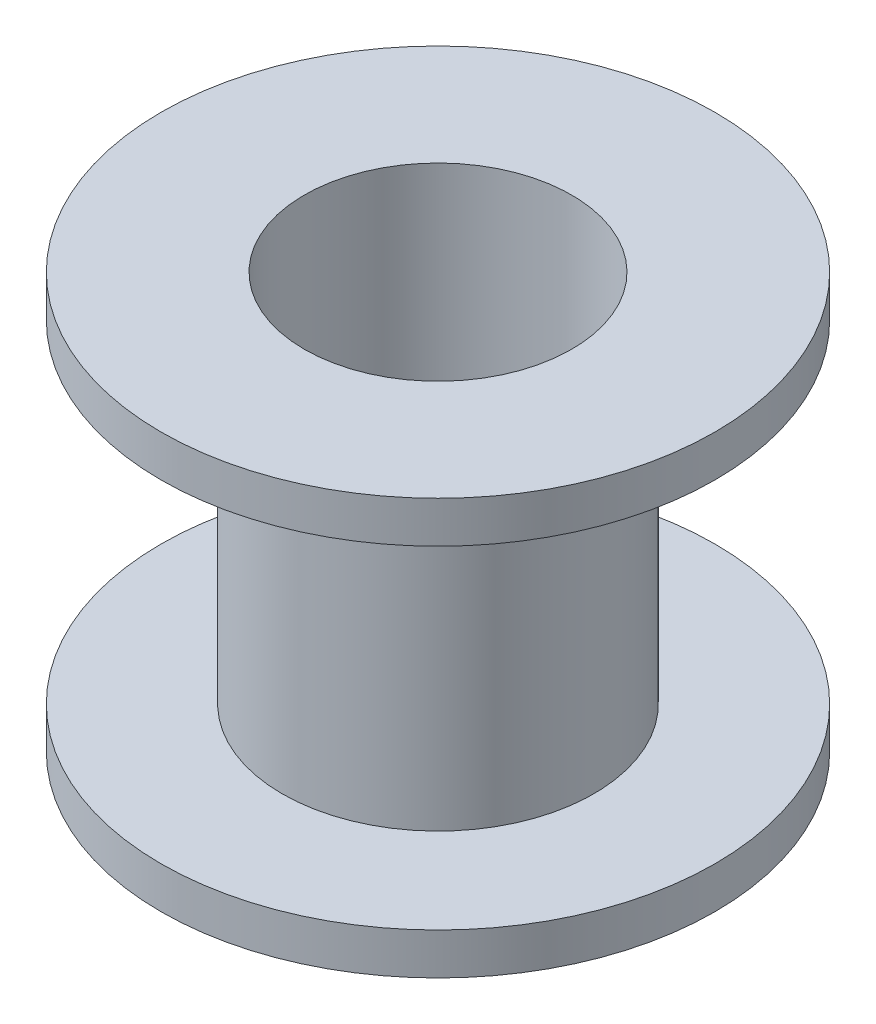
SolidWorks part; units mm, degrees
ref_plane "Front Plane" through (0, 0, 0) normal (0, 0, 1) x (1, 0, 0)
ref_plane "Top Plane" through (0, 0, 0) normal (0, 1, 0) x (1, 0, 0)
ref_plane "Right Plane" through (0, 0, 0) normal (1, 0, 0) x (0, 0, -1)
sketch "Sketch1" plane through (0, 0, 0) normal (0, 1, 0) x (1, 0, 0)
  circle A0 centre (0, 0) radius 4.826
  circle A1 centre (0, 0) radius 5.626
  dimension "715in" = 9.652
  dimension "D2" = 0.8
extrude "Boss-Extrude1" add sketch "Sketch1" along normal mid plane 15
sketch "Sketch2" plane through (0, 7.5, 0) normal (0, 1, 0) x (1, 0, 0)
  circle A0 centre (0, 0) radius 10
  circle A1 centre (0, 0) radius 10
  circle M3 centre (0, 0) radius 5.626
  dimension "D1" = 20
extrude "Boss-Extrude2" add sketch "Sketch2" against normal blind 1.5 contours A0 M3
mirror "Mirror1" about plane through (0, 0, 0) normal (0, 1, 0) of "Boss-Extrude2"
